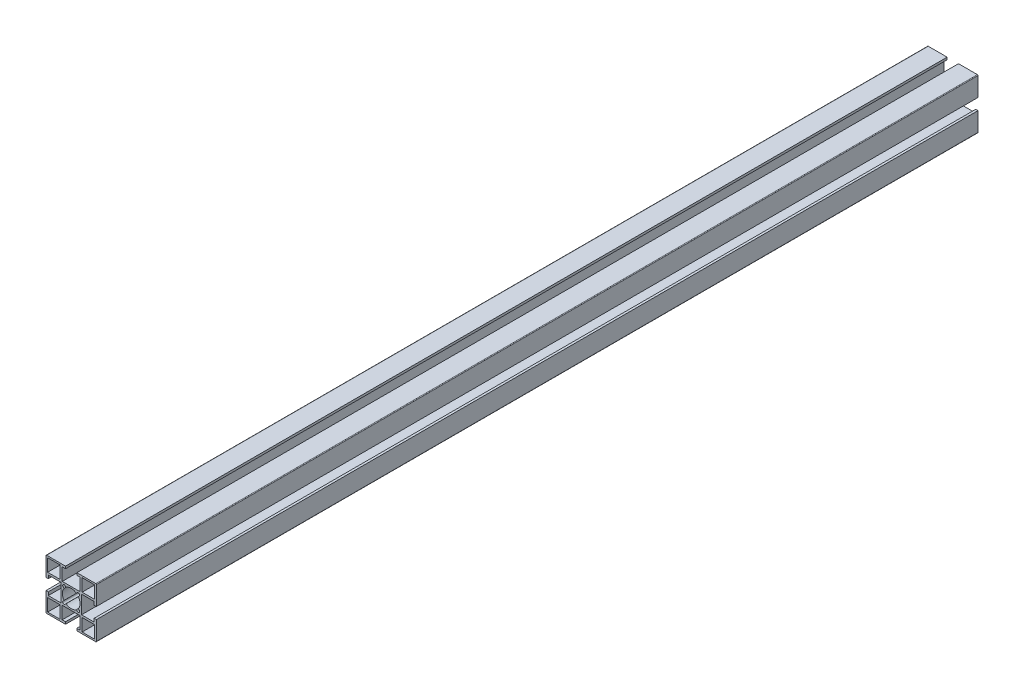
SolidWorks part; units mm, degrees
ref_plane "前视基准面" through (0, 0, 0) normal (0, 0, 1) x (1, 0, 0)
ref_plane "上视基准面" through (0, 0, 0) normal (0, 1, 0) x (1, 0, 0)
ref_plane "右视基准面" through (0, 0, 0) normal (1, 0, 0) x (0, 0, -1)
other "Configuration Table"
sketch "草图1" plane through (0, 0, 0) normal (1, 0, 0) x (0, 0, -1)
  line L0 (0, 0) -> (700, 0)
other "铝型材 40 X 40A X R0.5(1)"
ref_plane "基准面1" through (0, 0, 0) normal (0, 0, -1) x (0, 1, 0)
sketch "Sketch1" plane through (0, 0, 0) normal (0, 0, -1) x (0, 1, 0)
  line L0 (0, 0) -> (0, 16.3773) construction
  line L1 (0, 0) -> (-5.6569, 5.6569) construction
  line L2 (-19.5, 20) -> (-4.5, 20)
  line L3 (-20, 19.5) -> (-20, 4.5)
  line L4 (-19.5, -20) -> (-4.5, -20)
  line L5 (20, 19.5) -> (20, 4.5)
  line L6 (-4.879, 6.4347) -> (-4.1104, 5.6661)
  line L7 (-6.4347, 4.879) -> (-5.6661, 4.1104)
  line L8 (6.4347, 4.879) -> (5.6661, 4.1104)
  line L9 (0, 0) -> (20, 0) construction
  line L10 (4.879, 6.4347) -> (4.1104, 5.6661)
  line L11 (4.879, -6.4347) -> (4.1104, -5.6661)
  line L12 (6.4347, -4.879) -> (5.6661, -4.1104)
  line L13 (-6.4347, -4.879) -> (-5.6661, -4.1104)
  line L14 (-4.879, -6.4347) -> (-4.1104, -5.6661)
  line L15 (-4.5, 20) -> (-4.5, 18.2)
  line L16 (-18.7, 18.7) -> (-8.7, 18.7)
  line L17 (-18.7, 18.7) -> (-18.7, 8.7)
  line L18 (-18.7, 8.7) -> (-8.7, 8.7)
  line L19 (-8.7, 18.7) -> (-8.7, 8.7)
  line L20 (-7.1, 18.2) -> (-4.5, 18.2)
  line L21 (-7.1, 18.2) -> (-7.1, 8.2)
  line L22 (-7.1, 8.2) -> (7.1, 8.2)
  line L23 (7.1, 18.2) -> (7.1, 8.2)
  line L24 (4.5, 20) -> (4.5, 18.2)
  line L25 (4.5, 20) -> (19.5, 20)
  line L26 (4.5, 18.2) -> (7.1, 18.2)
  line L27 (8.7, 18.7) -> (8.7, 8.7)
  line L28 (18.7, 8.7) -> (8.7, 8.7)
  line L29 (18.7, 18.7) -> (18.7, 8.7)
  line L30 (18.7, 18.7) -> (8.7, 18.7)
  line L31 (18.2, 7.1) -> (8.2, 7.1)
  line L32 (18.2, 7.1) -> (18.2, 4.5)
  line L33 (20, 4.5) -> (18.2, 4.5)
  line L34 (8.2, 7.1) -> (8.2, -7.1)
  line L35 (18.2, -7.1) -> (8.2, -7.1)
  line L36 (18.2, -4.5) -> (18.2, -7.1)
  line L37 (20, -4.5) -> (18.2, -4.5)
  line L38 (7.1, -18.2) -> (7.1, -8.2)
  line L39 (7.1, -18.2) -> (4.5, -18.2)
  line L40 (4.5, -20) -> (4.5, -18.2)
  line L41 (7.1, -8.2) -> (-7.1, -8.2)
  line L42 (-7.1, -18.2) -> (-7.1, -8.2)
  line L43 (-4.5, -18.2) -> (-7.1, -18.2)
  line L44 (-4.5, -20) -> (-4.5, -18.2)
  line L45 (-18.2, -7.1) -> (-8.2, -7.1)
  line L46 (-18.2, -7.1) -> (-18.2, -4.5)
  line L47 (-20, -4.5) -> (-18.2, -4.5)
  line L48 (-8.2, -7.1) -> (-8.2, 7.1)
  line L49 (-18.2, 7.1) -> (-8.2, 7.1)
  line L50 (-18.2, 4.5) -> (-18.2, 7.1)
  line L51 (-20, 4.5) -> (-18.2, 4.5)
  line L52 (4.5, -20) -> (19.5, -20)
  line L53 (-20, -4.5) -> (-20, -19.5)
  line L54 (20, -4.5) -> (20, -19.5)
  line L55 (18.7, -18.7) -> (18.7, -8.7)
  line L56 (18.7, -8.7) -> (8.7, -8.7)
  line L57 (8.7, -18.7) -> (8.7, -8.7)
  line L58 (18.7, -18.7) -> (8.7, -18.7)
  line L59 (-8.7, -18.7) -> (-8.7, -8.7)
  line L60 (-18.7, -8.7) -> (-8.7, -8.7)
  line L61 (-18.7, -18.7) -> (-8.7, -18.7)
  line L62 (-18.7, -18.7) -> (-18.7, -8.7)
  arc A0 (-4.1104, 5.6661) -> (4.1104, 5.6661) centre (0, 0) cw
  arc A1 (-4.879, 6.4347) -> (-6.4347, 4.879) centre (-5.6569, 5.6569) ccw
  arc A2 (-4.1104, -5.6661) -> (4.1104, -5.6661) centre (0, 0) ccw
  arc A3 (-5.6661, 4.1104) -> (-5.6661, -4.1104) centre (0, 0) ccw
  arc A4 (6.4347, 4.879) -> (4.879, 6.4347) centre (5.6569, 5.6569) ccw
  arc A5 (4.879, -6.4347) -> (6.4347, -4.879) centre (5.6569, -5.6569) ccw
  arc A6 (-6.4347, -4.879) -> (-4.879, -6.4347) centre (-5.6569, -5.6569) ccw
  arc A7 (5.6661, 4.1104) -> (5.6661, -4.1104) centre (0, 0) cw
  arc A8 (-19.5, 20) -> (-20, 19.5) centre (-19.5, 19.5) ccw
  arc A9 (19.5, 20) -> (20, 19.5) centre (19.5, 19.5) cw
  arc A10 (19.5, -20) -> (20, -19.5) centre (19.5, -19.5) ccw
  arc A11 (-20, -19.5) -> (-19.5, -20) centre (-19.5, -19.5) ccw
  point P86 (20, 20)
  point P87 (-20, 20)
  point P88 (-20, -20)
  point P89 (20, -20)
  point P90 (0, 0)
  dimension "D2" = 7
  dimension "D3" = 45
  dimension "D4" = 1.1
  dimension "D5" = 1.8
  dimension "D6" = 8
  dimension "D7" = 1.3
  dimension "D8" = 14.2
  dimension "D10" = 10
  dimension "D11" = 10
  dimension "D12" = 40
  dimension "D13" = 9
  dimension "D14" = 0.5
  dimension "D9" = 1.3
